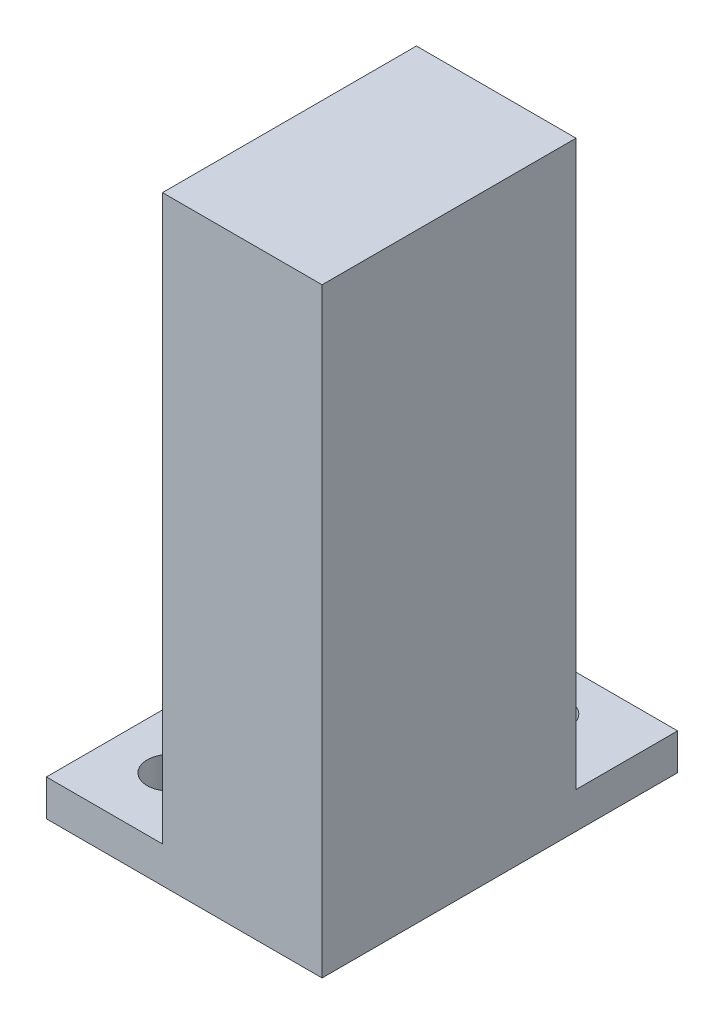
SolidWorks part; units mm, degrees
ref_plane "Front Plane" through (0, 0, 0) normal (0, 0, 1) x (1, 0, 0)
ref_plane "Top Plane" through (0, 0, 0) normal (0, 1, 0) x (1, 0, 0)
ref_plane "Right Plane" through (0, 0, 0) normal (1, 0, 0) x (0, 0, -1)
sketch "Sketch1" plane through (0, 0, 0) normal (0, 0, 1) x (1, 0, 0)
  line L0 (-11, 49.2197) -> (-11, -33.5303)
  line L2 (11, 49.2197) -> (11, -33.5303)
  line L3 (11, 49.2197) -> (-11, 49.2197)
  line L5 (-11, -33.5303) -> (11, -33.5303)
  circle A0 centre (0, 35.7197) radius 3.1
  circle A1 centre (0, 7.7197) radius 3.1
  dimension "D1" = 13.5
  dimension "D2" = 28
  dimension "D3" = 82.75
  dimension "D5" = 11
extrude "Boss-Extrude1" add sketch "Sketch1" along normal blind 30
sketch "Sketch2" plane through (0, 0, 30) normal (0, 0, 1) x (1, 0, 0)
  line L0 (-11, -33.5303) -> (11, -33.5303) construction
  line L2 (11, 49.2197) -> (-11, 49.2197) construction
  line L4 (-11, -33.5303) -> (11, -33.5303)
  line L5 (11, -33.5303) -> (11, 49.2197)
  line L6 (11, 49.2197) -> (-11, 49.2197)
  line L7 (-11, 49.2197) -> (-11, -33.5303)
extrude "Boss-Extrude2" add sketch "Sketch2" along normal blind 5
sketch "Sketch3" plane through (0, -33.5303, 0) normal (0, -1, 0) x (1, 0, 0)
  line L0 (-11, 0) -> (-27, 0)
  line L1 (-27, 0) -> (-27, 35)
  line L2 (-27, 35) -> (-11, 35)
  line L3 (-11, 0) -> (-11, -14)
  line L4 (-11, -14) -> (11, -14)
  line L5 (11, -14) -> (11, 0)
  line L6 (-11, 0) -> (11, 0)
  line L7 (-11, 0) -> (-11, 35)
  circle A0 centre (-19, 9) radius 3.1
  circle A1 centre (-19, 26) radius 3.1
  circle A2 centre (0, -7) radius 3.1
  line M4 (-11, 0) -> (11, 0)
  line M7 (-11, 35) -> (-11, 0)
  dimension "D1" = 6.2
  dimension "D2" = 6.2
  dimension "D3" = 9
  dimension "D4" = 9
  dimension "D6" = 6.2
  dimension "D7" = 11
  dimension "D5" = 14
extrude "Boss-Extrude3" add sketch "Sketch3" against normal blind 5 contours L2 L1 L0 A1 A0 M7 | L4 L5 L3 A2 M4
sketch "Sketch4" plane through (11, 0, 0) normal (1, 0, 0) x (0, 0, -1)
  line L6 (-35, -33.5303) -> (14, -33.5303)
  line L7 (14, -33.5303) -> (14, -28.5303)
  line L8 (14, -28.5303) -> (0, -28.5303)
  line L9 (0, -28.5303) -> (0, 49.2197)
  line L10 (0, 49.2197) -> (-35, 49.2197)
  line L11 (-35, 49.2197) -> (-35, -33.5303)
  line L12 (-35, -33.5303) -> (14, -33.5303)
  line L13 (14, -33.5303) -> (14, -28.5303)
  line L14 (14, -28.5303) -> (0, -28.5303)
  line L15 (0, -28.5303) -> (0, 49.2197)
  line L16 (0, 49.2197) -> (-35, 49.2197)
  line L17 (-35, 49.2197) -> (-35, -33.5303)
  dimension "D1" = 0
extrude "Boss-Extrude4" [suppressed] add sketch "Sketch4" along normal blind 2.5
